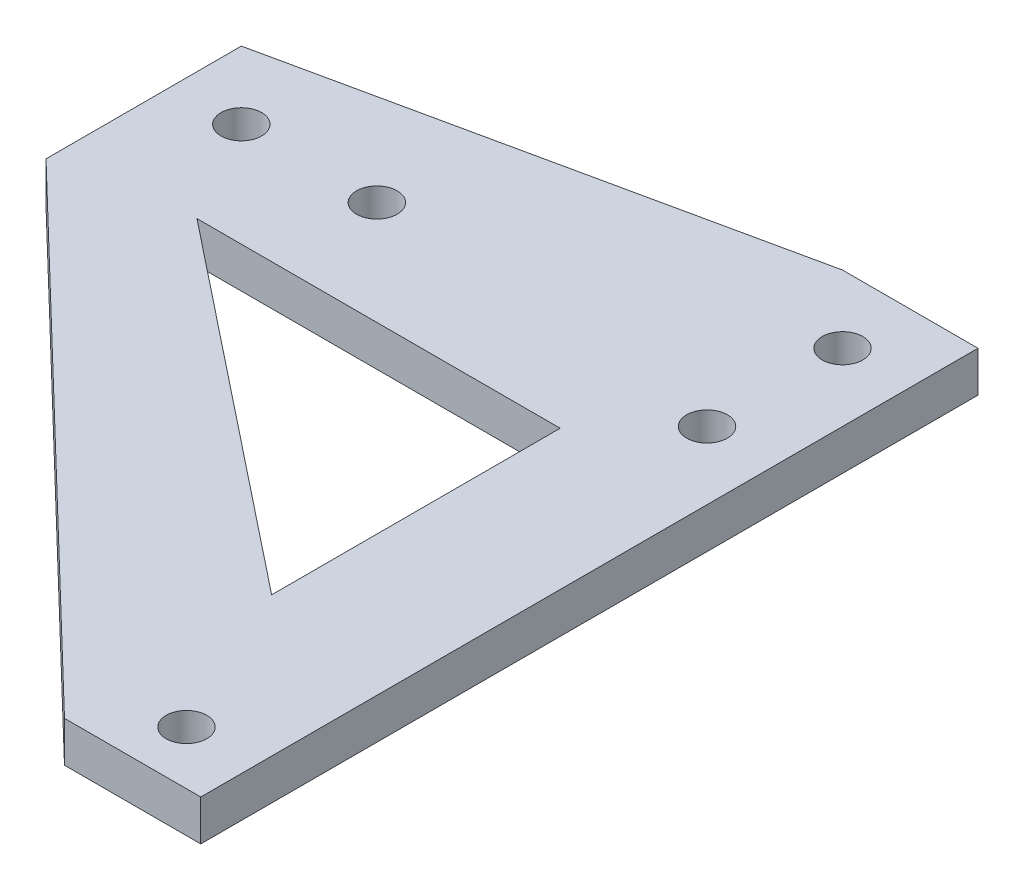
SolidWorks part; units mm, degrees
ref_plane "Front Plane" through (0, 0, 0) normal (0, 0, 1) x (1, 0, 0)
ref_plane "Top Plane" through (0, 0, 0) normal (0, 1, 0) x (1, 0, 0)
ref_plane "Right Plane" through (0, 0, 0) normal (1, 0, 0) x (0, 0, -1)
sketch "Sketch1" plane through (0, 0, 0) normal (0, 1, 0) x (1, 0, 0)
  line L0 (0, 0) -> (0, 10.18) construction
  line L1 (0, 10.18) -> (36.5, 10.18) construction
  line L2 (0, 0) -> (0, 51.73) construction
  line L3 (36.5, 10.18) -> (36.5, 49.6) construction
  line L4 (36.5, 49.6) -> (36.5, 59.6) construction
  line L5 (0, 0) -> (0, -5) construction
  line L7 (0, 51.73) -> (0, 56.73) construction
  line L8 (5, 56.73) -> (-5, 56.73)
  line L9 (-5, 56.73) -> (-5, -5)
  line L10 (5, 56.73) -> (5, 16.6667)
  line L11 (36.5, 59.6) -> (36.5, 64.6) construction
  line L12 (41.5, 64.6) -> (31.5, 64.6)
  line L13 (36.5, 10.18) -> (36.5, -19.82) construction
  line L15 (31.5, 64.6) -> (31.5, 16.6667)
  line L16 (41.5, 64.6) -> (41.5, -19.82)
  line L17 (31.5, 64.6) -> (-5, 56.73)
  line L18 (5, 56.73) -> (31.5, 54.48)
  line L19 (5, 16.6667) -> (31.5, 16.6667)
  line L20 (5, 5.234) -> (31.5, 5.234)
  line L21 (5, 5.234) -> (5, -5)
  line L22 (5, 5.234) -> (-5, 5.234)
  line L23 (-5, 5.234) -> (41.5, 5.234)
  line L24 (31.5, 5.234) -> (31.5, -19.82)
  line L25 (36.5, 10.18) -> (39.514, 10.18) construction
  line L26 (39.514, 10.18) -> (39.514, 11.18) construction
  line L27 (39.514, 11.18) -> (36.5, 11.18) construction
  circle A2 centre (0, 51.73) radius 1.5
  circle A3 centre (36.5, 49.6) radius 1.5
  circle A4 centre (36.5, 59.6) radius 1.5
  circle A5 centre (0, 10.18) radius 1.5
  circle A6 centre (36.5, 11.18) radius 1.5
  dimension "D1" = 10.18
  dimension "D2" = 36.5
  dimension "D3" = 51.73
  dimension "D4" = 39.42
  dimension "D5" = 10
  dimension "D6" = 5
  dimension "D12" = 1
  dimension "D7" = 5
  dimension "D8" = 5
  dimension "D9" = 5
  dimension "D10" = 5
  dimension "D11" = 5
extrude "Boss-Extrude1" add sketch "Sketch1" along normal blind 3
sketch "Sketch4" plane through (0, 3, 0) normal (0, 1, 0) x (1, 0, 0)
  line L0 (0, 51.73) -> (10, 51.73) construction
  circle A0 centre (10, 51.73) radius 1.5
extrude "Cut-Extrude2" cut sketch "Sketch4" against normal blind 7
sketch "Sketch5" plane through (0, 3, 0) normal (0, 1, 0) x (1, 0, 0)
  line L0 (-5, 5.234) -> (-5, 7.234) construction
  line L1 (-5, 56.73) -> (-5, 5.234) construction
  line L3 (-5, 7.234) -> (41.5, 7.234)
  line L4 (-5, 7.234) -> (-5, 5.234)
  line L5 (-5, 5.234) -> (41.5, 5.234)
  line L6 (41.5, 7.234) -> (41.5, 5.234)
  dimension "D1" = 2
extrude "Cut-Extrude3" cut sketch "Sketch5" against normal blind 7
sketch "Sketch6" plane through (0, 3, 0) normal (0, 1, 0) x (1, 0, 0)
  line L0 (31.4436, 7.234) -> (-5, 42.3128)
  line L1 (41.5, 7.234) -> (-5, 7.234) construction
  line L2 (-5, 56.73) -> (-5, 7.234) construction
  line L3 (-5, 42.3128) -> (-5, 7.234)
  line L4 (-5, 7.234) -> (31.4436, 7.234)
extrude "Cut-Extrude4" cut sketch "Sketch6" against normal blind 7
sketch "Sketch7" plane through (0, 3, 0) normal (0, 1, 0) x (1, 0, 0)
  line L0 (31.1931, 22.7729) -> (31.1931, 44.0664)
  line L1 (31.1931, 44.0664) -> (4.3883, 44.0664)
  line L2 (4.3883, 44.0664) -> (31.1931, 22.7729)
extrude "Cut-Extrude5" cut sketch "Sketch7" against normal blind 7
